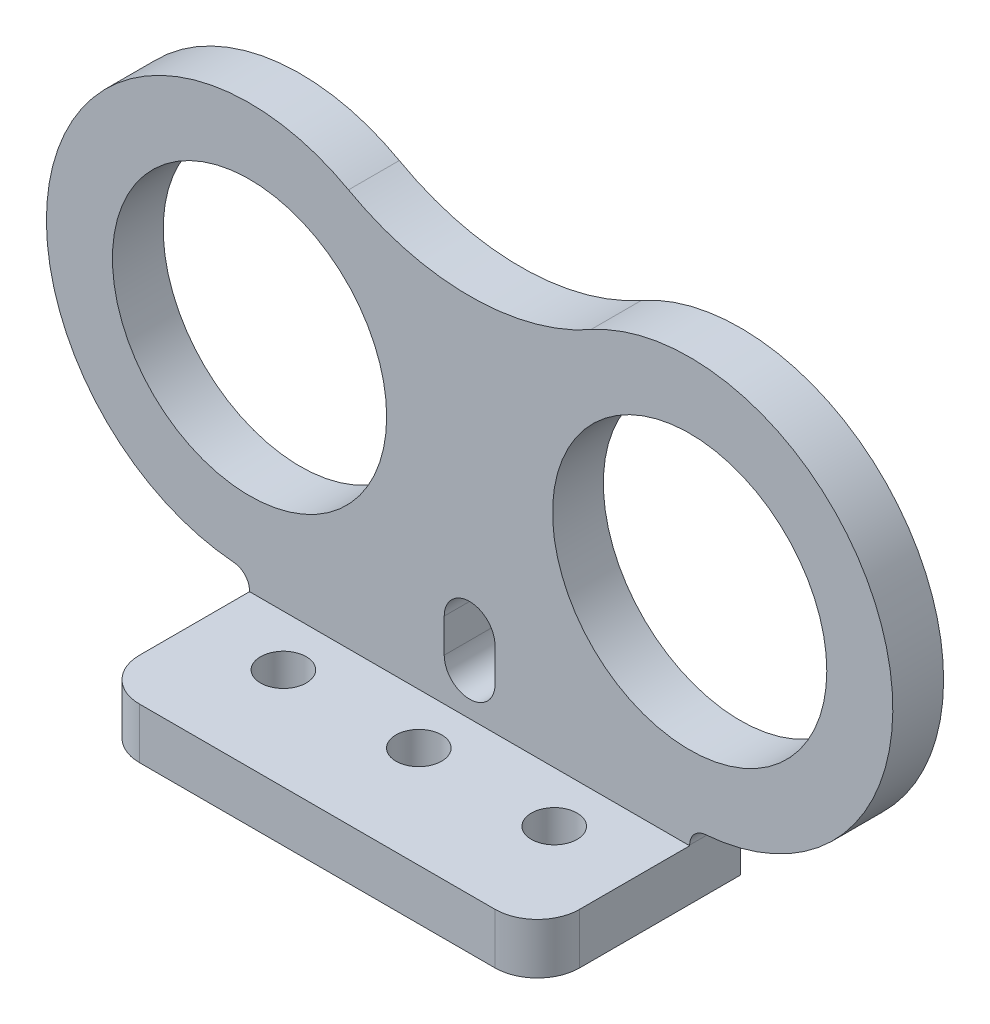
SolidWorks part; units mm, degrees
material "PA Type 6"
ref_plane "Front Plane" through (0, 0, 0) normal (0, 0, 1) x (1, 0, 0)
ref_plane "Top Plane" through (0, 0, 0) normal (0, 1, 0) x (1, 0, 0)
ref_plane "Right Plane" through (0, 0, 0) normal (1, 0, 0) x (0, 0, -1)
sketch "Sketch1" plane through (0, 0, 0) normal (0, 0, 1) x (1, 0, 0)
  line L0 (-25, 0) -> (25, 0)
  line L1 (25, 0) -> (25, 16)
  line L2 (0, 0) -> (0, 32) construction
  line L3 (25, 16) -> (-25, 16) construction
  line L4 (-25, 0) -> (-25, 16)
  line L5 (-13, 3.0385) -> (-13, 0)
  line L6 (13, 3.0385) -> (13, 0)
  line L7 (0, 7.5) -> (0, 5.5) construction
  line L8 (1.5, 7.5) -> (1.5, 5.5)
  line L9 (-1.5, 7.5) -> (-1.5, 5.5)
  circle A0 centre (13, 16) radius 8.1
  arc A1 (25, 16) -> (7.1534, 26.4793) centre (13, 16) ccw
  arc A2 (-25, 16) -> (-7.1534, 26.4793) centre (-13, 16) cw
  circle A3 centre (-13, 16) radius 8.1
  arc A4 (-7.1534, 26.4793) -> (7.1534, 26.4793) centre (0, 39.3008) ccw
  arc A5 (-25, 16) -> (-13.9231, 4.0356) centre (-13, 16) ccw
  arc A6 (-13.9231, 4.0356) -> (-13, 3.0385) centre (-14, 3.0385) cw
  arc A7 (25, 16) -> (13.9231, 4.0356) centre (13, 16) cw
  arc A8 (13.9231, 4.0356) -> (13, 3.0385) centre (14, 3.0385) ccw
  arc A9 (1.5, 7.5) -> (-1.5, 7.5) centre (0, 7.5) ccw
  arc A10 (-1.5, 5.5) -> (1.5, 5.5) centre (0, 5.5) ccw
  point P10 (0, 16)
  point P25 (0, 6.5)
  dimension "D2" = 16.2
  dimension "D5" = 1
  dimension "D1" = 25
  dimension "D3" = 13
  dimension "D4" = 16
  dimension "D6" = 3
  dimension "D7" = 2
  dimension "D8" = 6.5
extrude "Boss-Extrude1" add sketch "Sketch1" along normal blind 3 contours A8 A7 A1 A4 A2 A5 A6 L5 L0 L6 A0 A3
sketch "Sketch3" plane through (0, 0, 0) normal (0, -1, 0) x (1, 0, 0)
  line L0 (0, 12) -> (0, 0) construction
  line L1 (-13, 3) -> (13, 3)
  line L2 (-13, 3) -> (-13, 9.5)
  line L3 (-10.5, 12) -> (10.5, 12)
  line L4 (13, 3) -> (13, 9.5)
  line L5 (0, 6) -> (8, 6) construction
  circle A0 centre (8, 6) radius 1.35
  circle A1 centre (-8, 6) radius 1.35
  arc A2 (-13, 9.5) -> (-10.5, 12) centre (-10.5, 9.5) cw
  arc A3 (10.5, 12) -> (13, 9.5) centre (10.5, 9.5) cw
  circle A4 centre (0, 6) radius 1.35
  point P18 (13, 12)
  dimension "D3" = 2.7
  dimension "D4" = 2.5
  dimension "D5" = 2.7
  dimension "D1" = 9
  dimension "D2" = 8
extrude "Boss-Extrude2" add sketch "Sketch3" against normal blind 3
